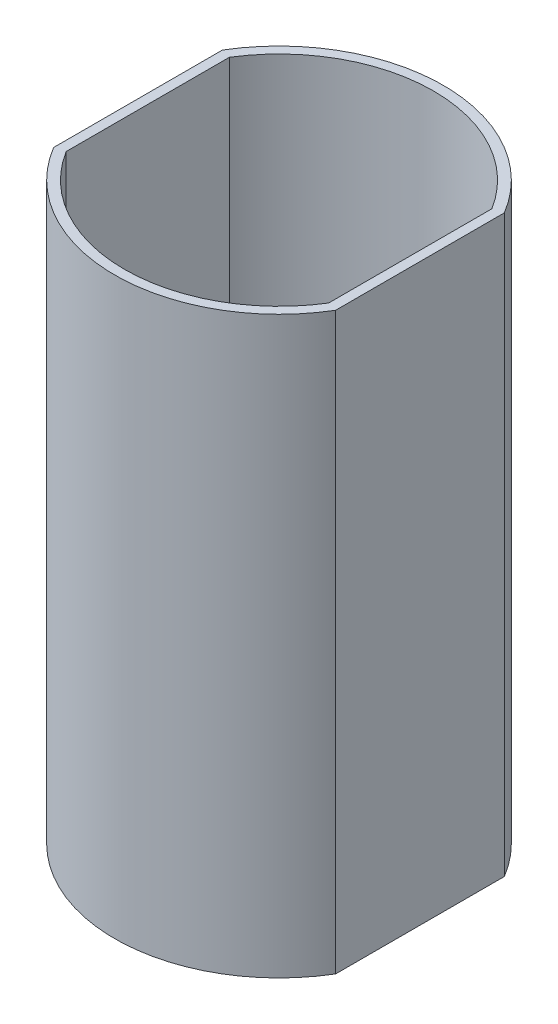
SolidWorks part; units mm, degrees
ref_plane "Front Plane" through (0, 0, 0) normal (0, 0, 1) x (1, 0, 0)
ref_plane "Top Plane" through (0, 0, 0) normal (0, 1, 0) x (1, 0, 0)
ref_plane "Right Plane" through (0, 0, 0) normal (1, 0, 0) x (0, 0, -1)
sketch "Sketch1" plane through (0, 0, 0) normal (0, 1, 0) x (1, 0, 0)
  circle A1 centre (0, 0) radius 30.3
  dimension "D2" = 60.6
extrude "Boss-Extrude1" add sketch "Sketch1" along normal blind 106
sketch "Sketch2" plane through (0, 106, 0) normal (0, 1, 0) x (1, 0, 0)
  line L0 (0, 30.3) -> (0, -30.3) construction
  line L1 (0, 30.3) -> (-26, 30.3) construction
  line L2 (-26, 30.3) -> (-26, -30.3) construction
  line L3 (-26, -30.3) -> (0, -30.3) construction
  line L4 (26, -30.3) -> (31, -30.3)
  line L5 (-26, 30.3) -> (-31, 30.3)
  line L6 (-26, 30.3) -> (-26, -30.3)
  line L7 (-26, -30.3) -> (-31, -30.3)
  line L8 (-31, 30.3) -> (-31, -30.3)
  line L9 (31, 30.3) -> (31, -30.3)
  line L10 (26, 30.3) -> (31, 30.3)
  line L11 (26, 30.3) -> (26, -30.3)
  circle A0 centre (0, 0) radius 30.3 construction
  dimension "D1" = 26
  dimension "D2" = 5
extrude "Cut-Extrude1" cut sketch "Sketch2" against normal up to next
shell "Shell1" thickness 1.8
sketch "Sketch3" plane through (0, 1.8, 0) normal (0, 1, 0) x (1, 0, 0)
  line L0 (0, 0) -> (0, 28.5) construction
  line L1 (-24.2, 0) -> (24.2, 0) construction
  line L2 (-24.2, -15.0536) -> (-24.2, 15.0536) construction
  line L3 (24.2, 15.0536) -> (24.2, -15.0536) construction
  arc A0 (24.2, 15.0536) -> (-24.2, 15.0536) centre (0, 0) ccw construction
  circle A1 centre (0, 23.5) radius 1.75
  circle A2 centre (0, -23.5) radius 1.75
  circle A3 centre (0, 0) radius 7.5
  dimension "D1" = 3.5
  dimension "D2" = 5
  dimension "D3" = 15
extrude "Cut-Extrude2" cut sketch "Sketch3" against normal up to next
sketch "Sketch4" plane through (0, 1.8, 0) normal (0, 1, 0) x (1, 0, 0)
  line L0 (0, 28.5) -> (0, 0) construction
  line L1 (-24.2, 0) -> (24.2, 0) construction
  line L2 (-24.2, -15.0536) -> (-24.2, 15.0536) construction
  line L3 (24.2, 15.0536) -> (24.2, -15.0536) construction
  line L4 (0, 28.5) -> (3.5, 28.5) construction
  line L5 (-3.5, -28.5) -> (3.5, -20.5) construction
  line L6 (-3.5, 20.5) -> (3.5, 20.5)
  line L7 (-3.5, 20.5) -> (-3.5, 28.5)
  line L8 (-3.5, 28.5) -> (3.5, 28.5)
  line L9 (3.5, 20.5) -> (3.5, 28.5)
  line L10 (-3.5, 20.5) -> (3.5, 28.5) construction
  line L11 (-3.5, 28.5) -> (3.5, 20.5) construction
  line L12 (-3.5, -20.5) -> (3.5, -28.5) construction
  line L13 (0, -28.5) -> (3.5, -28.5) construction
  line L14 (3.5, -20.5) -> (3.5, -28.5)
  line L15 (-3.5, -28.5) -> (3.5, -28.5)
  line L16 (-3.5, -20.5) -> (-3.5, -28.5)
  line L17 (-3.5, -20.5) -> (3.5, -20.5)
  arc A0 (24.2, 15.0536) -> (-24.2, 15.0536) centre (0, 0) ccw construction
  circle A1 centre (0, 23.5) radius 1.75
  circle A2 centre (0, -23.5) radius 1.75
  point P12 (0, 24.5)
  point P27 (0, -24.5)
  dimension "D3" = 3.5
  dimension "D1" = 3.5
  dimension "D2" = 8
extrude "Boss-Extrude2" add sketch "Sketch4" along normal blind 15
